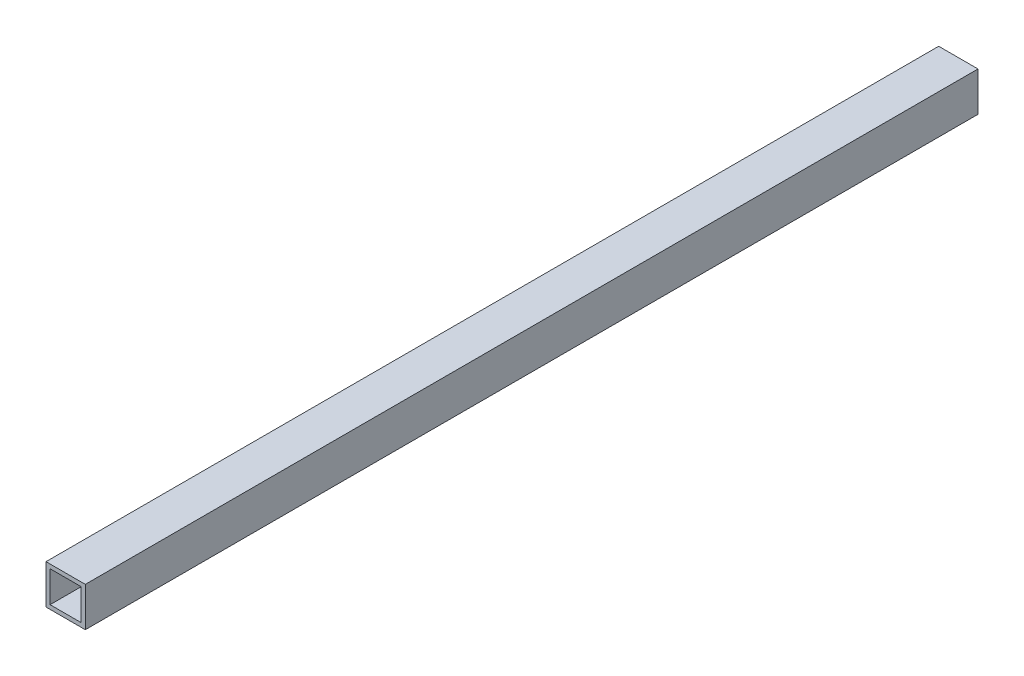
SolidWorks part; units mm, degrees
ref_plane "前视基准面" through (0, 0, 0) normal (0, 0, 1) x (1, 0, 0)
ref_plane "上视基准面" through (0, 0, 0) normal (0, 1, 0) x (1, 0, 0)
ref_plane "右视基准面" through (0, 0, 0) normal (1, 0, 0) x (0, 0, -1)
sketch "草图1" plane through (0, 0, 0) normal (0, 0, 1) x (1, 0, 0)
  line L0 (2.5, 2.5) -> (21.5, 2.5)
  line L1 (0, 0) -> (24, 0)
  line L2 (0, 0) -> (0, 24)
  line L3 (0, 24) -> (24, 24)
  line L4 (24, 0) -> (24, 24)
  line L5 (21.5, 2.5) -> (21.5, 21.5)
  line L6 (2.5, 21.5) -> (21.5, 21.5)
  line L7 (2.5, 2.5) -> (2.5, 21.5)
  dimension "D1" = 2.5
extrude "凸台-拉伸1" add sketch "草图1" along normal blind 545
